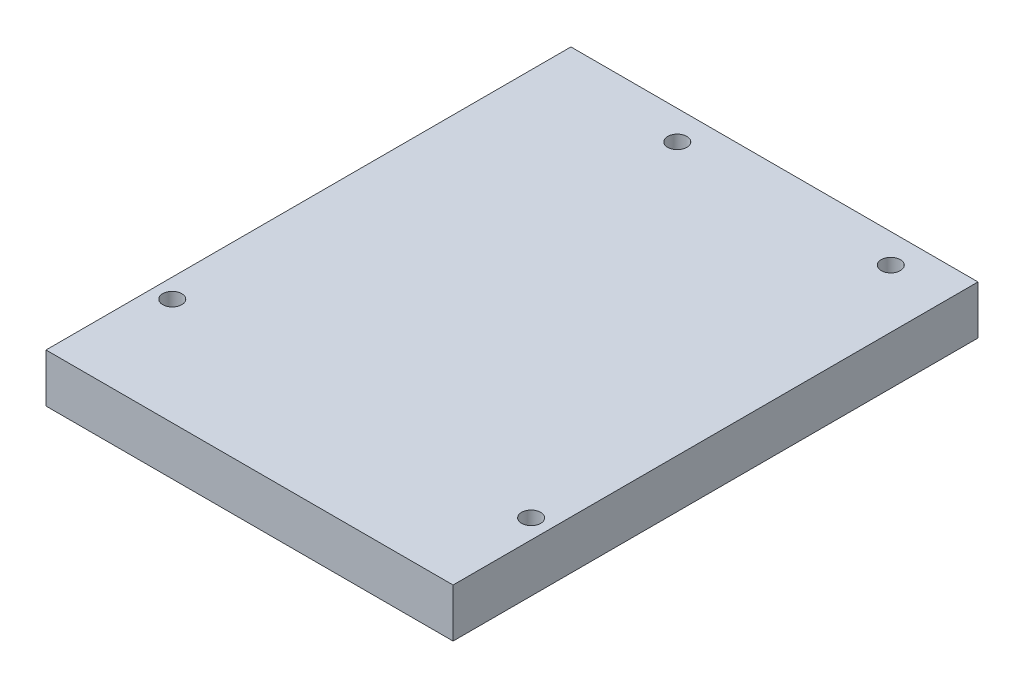
SolidWorks part; units mm, degrees
ref_plane "Front Plane" through (0, 0, 0) normal (0, 0, 1) x (1, 0, 0)
ref_plane "Top Plane" through (0, 0, 0) normal (0, 1, 0) x (1, 0, 0)
ref_plane "Right Plane" through (0, 0, 0) normal (1, 0, 0) x (0, 0, -1)
sketch "Sketch1" plane through (0, 0, 0) normal (0, 1, 0) x (1, 0, 0)
  line L0 (-50.7, 14) -> (-2.5, 14) construction
  line L1 (-2.5, 14) -> (-2.5, 12.7) construction
  line L2 (-35.5, 64.8) -> (-35.5, 14) construction
  line L4 (-35.5, 64.8) -> (-7.6, 64.8) construction
  line L5 (-53.2, 68.6) -> (0, 68.6)
  line L6 (-53.2, 68.6) -> (-53.2, 0)
  line L7 (-53.2, 0) -> (0, 0)
  line L8 (0, 68.6) -> (0, 0)
  circle A2 centre (-35.5, 64.8) radius 1.25
  circle A3 centre (-7.6, 64.8) radius 1.25
  circle A4 centre (-50.7, 14) radius 1.25
  circle A5 centre (-2.5, 12.7) radius 1.25
  dimension "D4" = 2.5
  dimension "D2" = 48.2
  dimension "D3" = 1.3
  dimension "D5" = 53.2
  dimension "D6" = 50.8
  dimension "D7" = 15.2
  dimension "D8" = 27.9
  dimension "D9" = 14
  dimension "D10" = 68.6
  dimension "D11" = 2.5
extrude "Boss-Extrude1" add sketch "Sketch1" along normal blind 6.35
